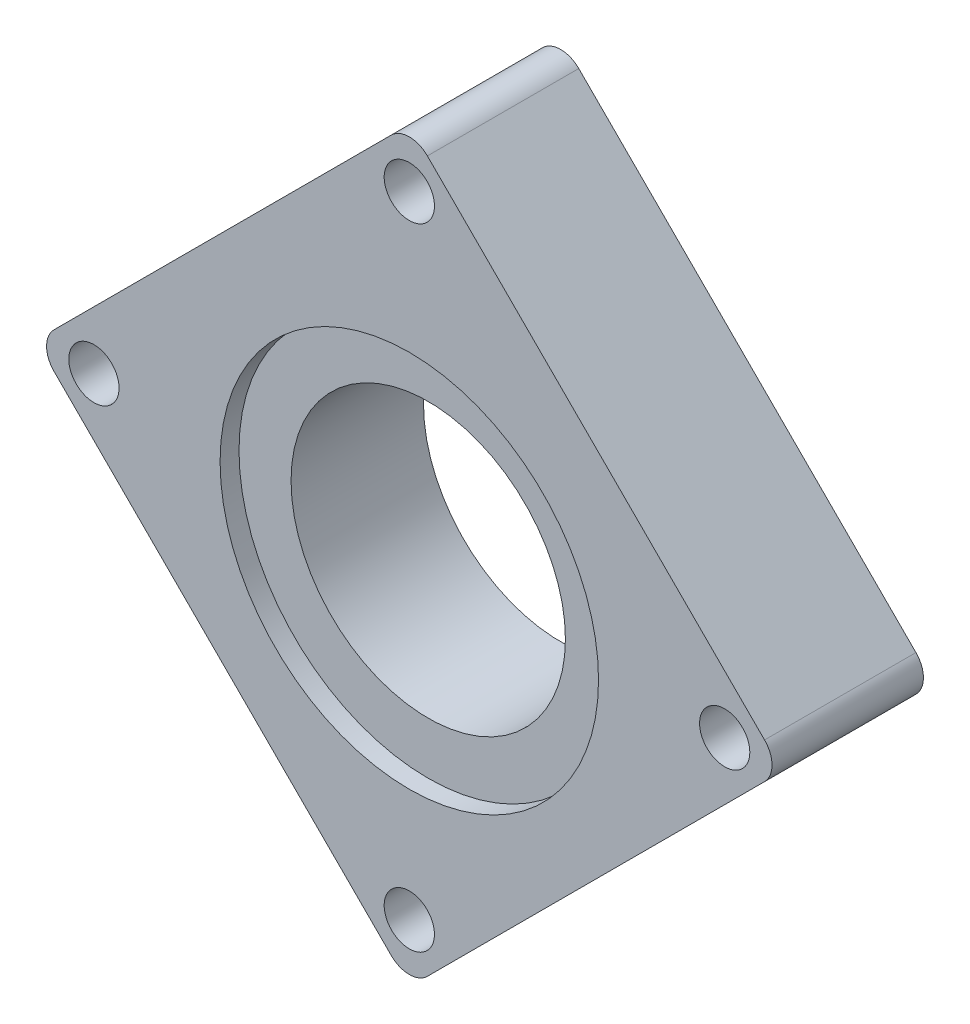
SolidWorks part; units mm, degrees
ref_plane "Front Plane" through (0, 0, 0) normal (0, 0, 1) x (1, 0, 0)
ref_plane "Top Plane" through (0, 0, 0) normal (0, 1, 0) x (1, 0, 0)
ref_plane "Right Plane" through (0, 0, 0) normal (1, 0, 0) x (0, 0, -1)
sketch "Sketch1" plane through (0, 0, 0) normal (0, 0, 1) x (1, 0, 0)
  line L48 (96.4567, 48.3669) -> (64.849, 79.9745)
  line L49 (92.4262, 40.518) -> (96.4567, 44.5485)
  line L52 (60.8185, 8.9103) -> (92.4262, 40.518)
  line L53 (52.9697, 12.9408) -> (57.0002, 8.9103)
  line L56 (21.362, 44.5485) -> (52.9697, 12.9408)
  line L57 (25.3925, 52.3974) -> (21.362, 48.3669)
  line L60 (57.0002, 84.0051) -> (25.3925, 52.3974)
  line L61 (64.849, 79.9745) -> (60.8185, 84.0051)
  circle A0 centre (58.9094, 45.0773) radius 14.5
  circle A12 centre (58.9094, 13.1247) radius 2.6556
  circle A13 centre (92.2424, 46.4577) radius 2.6556
  circle A14 centre (58.9094, 79.7907) radius 2.6556
  circle A15 centre (25.5763, 46.4577) radius 2.6556
  arc A31 (96.4567, 44.5485) -> (96.4567, 48.3669) centre (94.5475, 46.4577) ccw
  arc A33 (57.0002, 8.9103) -> (60.8185, 8.9103) centre (58.9094, 10.8195) ccw
  arc A35 (21.362, 48.3669) -> (21.362, 44.5485) centre (23.2712, 46.4577) ccw
  arc A37 (60.8185, 84.0051) -> (57.0002, 84.0051) centre (58.9094, 82.0959) ccw
  dimension "D1" = 29
extrude "Boss-Extrude1" add sketch "Sketch1" along normal blind 16
sketch "Sketch2" plane through (0, 0, 16) normal (0, 0, 1) x (1, 0, 0)
  circle A0 centre (58.9094, 45.0773) radius 20
extrude "Cut-Extrude1" cut sketch "Sketch2" against normal blind 2
